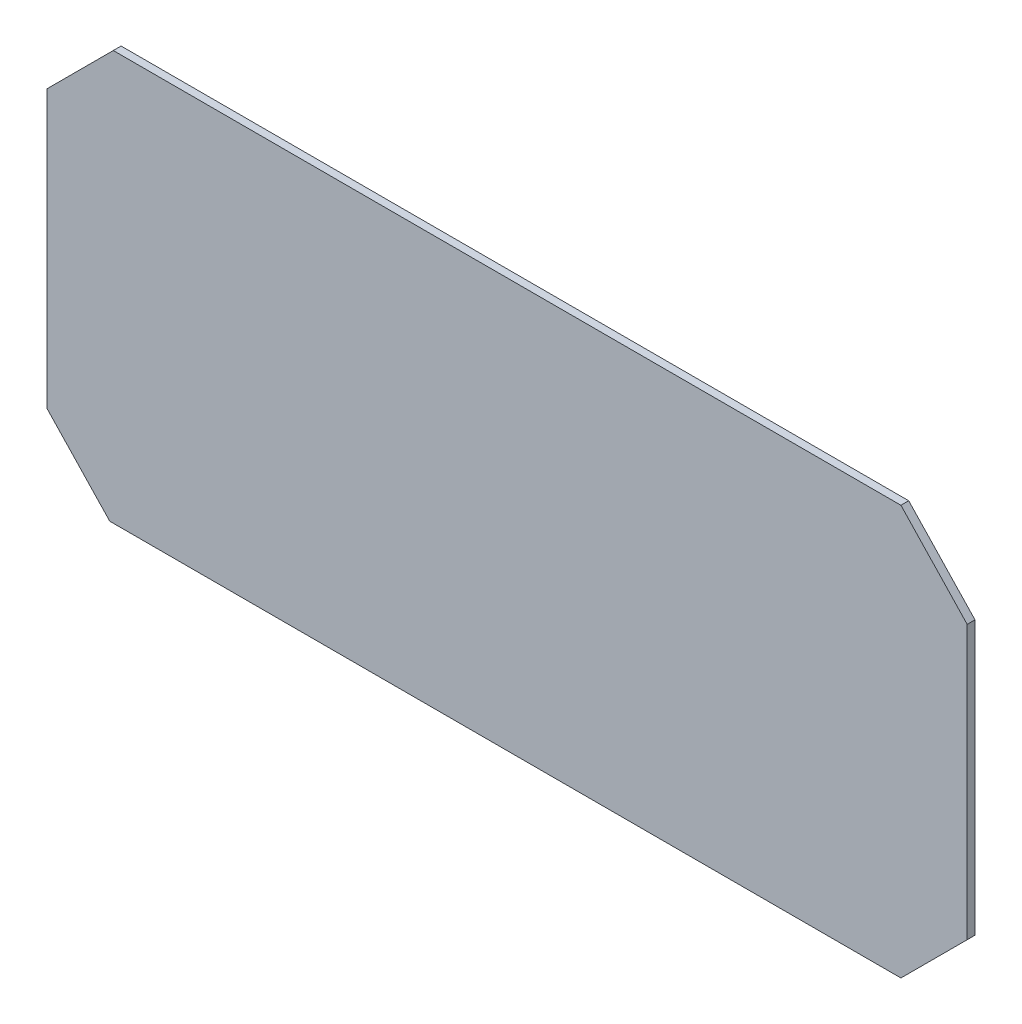
SolidWorks part; units mm, degrees
material "A286 Superalliage à base de fer"
ref_plane "Plan de face" through (0, 0, 0) normal (0, 0, 1) x (1, 0, 0)
ref_plane "Plan de dessus" through (0, 0, 0) normal (0, 1, 0) x (1, 0, 0)
ref_plane "Plan de droite" through (0, 0, 0) normal (1, 0, 0) x (0, 0, -1)
sketch "Esquisse1" plane through (0, 0, 0) normal (0, 0, 1) x (1, 0, 0)
  line L1 (0, 0) -> (236, 0) construction
  line L2 (0, 0) -> (0, -105) construction
  line L3 (0, -105) -> (236, -105) construction
  line L4 (236, 0) -> (236, -105) construction
  line L8 (0, -17) -> (0, -88)
  line L9 (0, -88) -> (16.0933, -105)
  line L10 (16.0933, -105) -> (219, -105)
  line L11 (219, -105) -> (236, -88)
  line L12 (236, -88) -> (236, -17.9578)
  line L13 (236, -17.9578) -> (219, 0)
  line L14 (219, 0) -> (17, 0)
  line L15 (17, 0) -> (0, -17)
  dimension "D1" = 236
  dimension "D2" = 105
  dimension "D3" = 16.0933
  dimension "D4" = 17
  dimension "D5" = 17
  dimension "D6" = 17
  dimension "D7" = 17
  dimension "D8" = 17
  dimension "D9" = 17
extrude "Boss.-Extru.1" add sketch "Esquisse1" along normal blind 2
